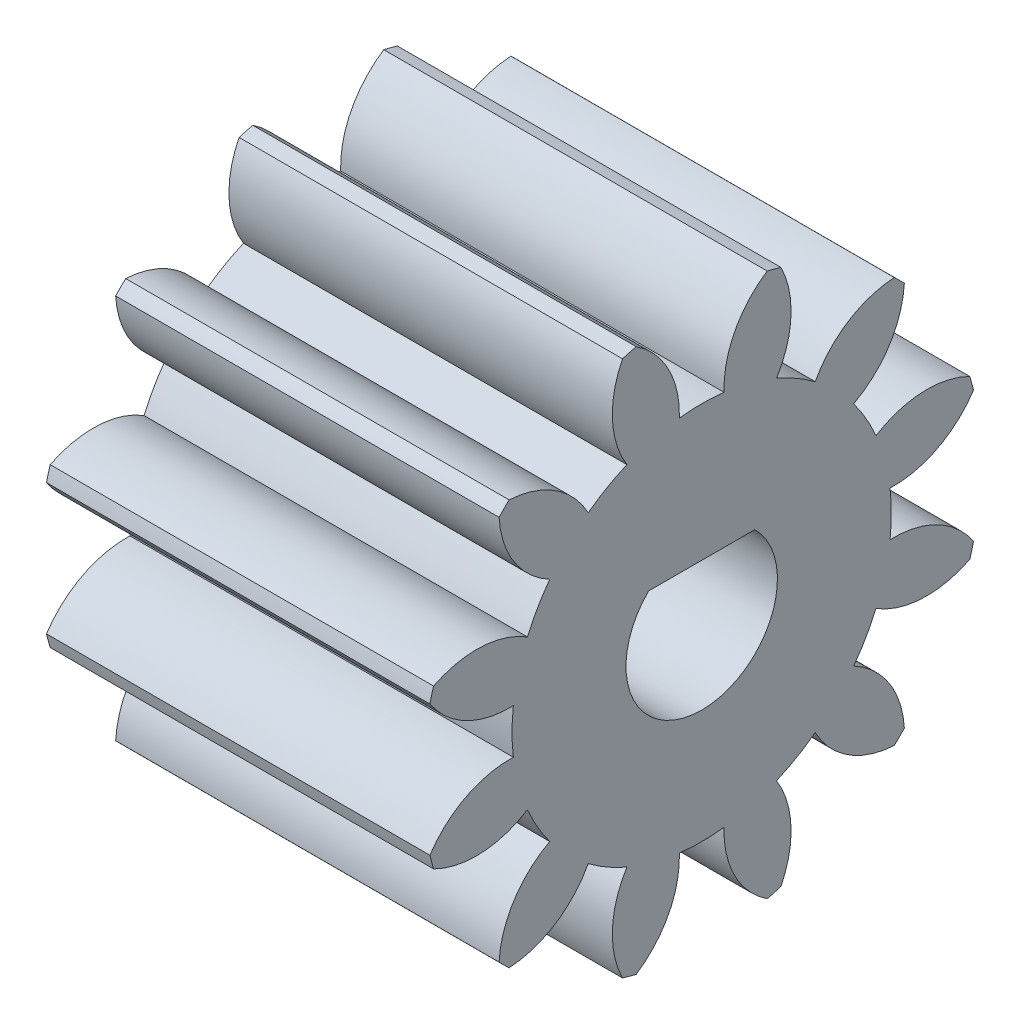
SolidWorks part; units mm, degrees
ref_plane "Plane1" through (0, 0, 0) normal (0, 0, 1) x (1, 0, 0)
ref_plane "Plane2" through (0, 0, 0) normal (0, 1, 0) x (1, 0, 0)
ref_plane "Plane3" through (0, 0, 0) normal (1, 0, 0) x (0, 0, -1)
sketch "HoldingSke" plane through (0, 0, 0) normal (0, 1, 0) x (1, 0, 0)
  line L0 (0, 0) -> (0.7825, -0.1663)
  line L1 (-15, 0) -> (100, 0) construction
  line L2 (0, 0) -> (-2.1039, 2.3779)
  line L3 (0, 0) -> (-11.863, 4.5341)
  line L4 (0, 0) -> (8.4473, 1.7955)
  line L5 (0, 0) -> (-46.8476, -17.4728)
  line L6 (0, 0) -> (-9.9476, -6.7116)
  line L7 (-2.1039, 2.3779) -> (8.6586, 51.2059)
  line L8 (-76.2, 54.61) -> (-76.1, 54.61)
  line L9 (-71.009, 38.7566) -> (-53.1078, 45.2721)
  line L10 (-76.2, 71.12) -> (104.1128, 71.12)
  line L11 (0, 0) -> (-12, 0)
  line L12 (-76.2, 101.6) -> (-76.155, 101.6)
  line L13 (24.9733, 27.94) -> (52.9518, 28.4284)
  line L14 (24.9733, 27.94) -> (24.9743, 27.94)
  line L15 (24.9733, 27.94) -> (100.4006, 29.5858)
  line L16 (-63.627, -1.25) -> (-12.827, -1.25)
  circle A0 centre (0, 0) radius 0.4
  circle A1 centre (0, 0) radius 5.9365
  circle A2 centre (0, 0) radius 37.5
  circle A3 centre (0, 0) radius 0.4
  dimension "MHD" = 11.873
  dimension "Hub_dia" = 75
  dimension "Bore" = 0.8
  dimension "MBD" = 0.8
  dimension "Num_teeth" = 12
  dimension "Pitch_radius" = 180.3128
  dimension "Pitch" = 0.8
  dimension "Width" = 12
  dimension "Overall_len" = 50
  dimension "Show_teeth" = 12
  dimension "Thickness" = 12
  dimension "OAL" = 50.0001
  dimension "T_dim" = 0.1
  dimension "Ap" = 20
  dimension "H" = 19.05
  dimension "Backlash" = 0.045
  dimension "Addendum_fac" = 1
  dimension "Dedendum_fac" = 1.25
  dimension "Clearance_fac" = 0.25
  dimension "Dedendum_add" = 0.001
  dimension "Module" = 1.25
sketch "BasProSke" plane through (0, 0, 0) normal (0, 1, 0) x (1, 0, 0)
  line L0 (-10, 0) -> (60, 0) construction
  line L1 (0, 0) -> (0, 8.75)
  line L2 (0, 0) -> (12, 0)
  line L3 (12, 0) -> (12, 8.75)
  line L4 (12, 8.75) -> (0, 8.75)
  dimension "Diameter" = 17.5
  dimension "Thickness" = 12
revolve "Base-Revolve" add sketch "BasProSke" angle 360 about L0
sketch "TooCutSke" plane through (0, 0, 0) normal (1, 0, 0) x (0, 0, -1)
  line L1 (0, 0) -> (0, 107) construction
  line L2 (0, 0) -> (-1.0576, 7.4251) construction
  line L3 (0, 0) -> (-3.8542, 14.3841) construction
  line L4 (-1.0576, 7.4251) -> (-1.9271, 7.1921) construction
  arc A0 (0.6993, 5.8952) -> (-0.6993, 5.8952) centre (0, 0) ccw
  arc A1 (2.0786, 8.5257) -> (-2.0786, 8.5257) centre (0, 0) ccw
  circle A2 centre (0, 0) radius 7.5 construction
  circle A3 centre (0, 0) radius 7.0477 construction
  arc A4 (-0.6993, 5.8952) -> (-2.0786, 8.5257) centre (-3.6975, 5.9999) ccw
  arc A5 (2.0786, 8.5257) -> (0.6993, 5.8952) centre (3.6975, 5.9999) ccw
  dimension "Root_dia" = 11.873
  dimension "Overcut_dia" = 17.5508
  dimension "Pitch_dia" = 15
  dimension "Base_dia" = 14.0954
  dimension "Flank_rad" = 3
  dimension "Half_ang" = 15
  dimension "Half_CT" = 0.9002
extrude "ToothCut" cut sketch "TooCutSke" along normal through all
fillet "Breaks" [suppressed] radius 0.025
fillet "RootFillets" [suppressed] radius 0.3135
pattern_circular "TeethCuts" count 12 every 30 about axis through (-10, 0, 0) along (1, 0, 0) of "ToothCut", "RootFillets", "Breaks"
sketch "HubNeaOneSke" plane through (0, 0, 0) normal (-1, 0, 0) x (0, 0, 1)
  circle A0 centre (0, 0) radius 5.9365
  dimension "Diameter" = 11.873
extrude "HubNearOne" [suppressed] add sketch "HubNeaOneSke" along normal blind 38.0001
sketch "HubNeaBotSke" plane through (0, 0, 0) normal (-1, 0, 0) x (0, 0, 1)
  circle A0 centre (0, 0) radius 5.9365
  dimension "Diameter" = 11.873
extrude "HubNearBoth" [suppressed] add sketch "HubNeaBotSke" along normal blind 19
ref_plane "FarPln" through (12, 0, 0) normal (1, 0, 0) x (0, 0, -1)
sketch "HubFarSke" plane through (12, 0, 0) normal (1, 0, 0) x (0, 0, -1)
  circle A0 centre (0, 0) radius 5.9365
  dimension "Diameter" = 11.873
extrude "HubFar" [suppressed] add sketch "HubFarSke" along normal blind 19
sketch "BorSke" plane through (0, 0, 0) normal (1, 0, 0) x (0, 0, -1)
  circle A0 centre (0, 0) radius 0.4
  dimension "Diameter" = 0.8
extrude "Bore" cut sketch "BorSke" along normal mid plane 100.0001
sketch "KeySke" plane through (0, 0, 0) normal (1, 0, 0) x (0, 0, -1)
  line L0 (-0.05, 0) -> (-0.05, 0.5)
  line L1 (-0.05, 0.5) -> (0.05, 0.5)
  line L2 (0.05, 0.5) -> (0.05, 0)
  line L3 (0, 0) -> (0, 34) construction
  line L4 (-0.05, 0) -> (0.05, 0)
  dimension "Offset" = 0.5
  dimension "Width" = 0.1
extrude "Keyway" [suppressed] cut sketch "KeySke" along normal mid plane 100.0001
pattern_circular "Keyway2" [suppressed] count 2 every 90 about axis through (-10, 0, 0) along (1, 0, 0)
sketch "Sketch1" plane through (12, 0, 0) normal (1, 0, 0) x (0, 0, -1)
  line L0 (-1.6616, 1.69) -> (1.6616, 1.69)
  arc A0 (-1.6616, 1.69) -> (1.6616, 1.69) centre (0, 0) ccw
  point P5 (0, -2.37)
  dimension "D1" = 4.74
  dimension "D2" = 4.06
extrude "Cut-Extrude1" cut sketch "Sketch1" against normal through all
equation "' \"Module@HoldingSke\" = 6.35"
equation "' \"Num_teeth@HoldingSke\" = 12"
equation "' \"Ap@HoldingSke\" =  20"
equation "' \"Width@HoldingSke\" = 0.5 * 25.4"
equation "' \"Hub_dia@HoldingSke\"= 1 * 25.4"
equation "' \"Overall_len@HoldingSke\" = 1.0 * 25.4"
equation "' \"Bore@HoldingSke\" = 0.75 * 25.4"
equation "' \"T_dim@HoldingSke\" = 0.1 * 25.4"
equation "' \"Width@KeySke\" = 0.25 * 25.4"
equation "' \"Show_teeth@HoldingSke\" = 13"
equation "' \"Backlash@HoldingSke\" = 0.009 * 25.4"
equation "' \"Addendum_fac@HoldingSke\" = 1.0"
equation "' \"Dedendum_fac@HoldingSke\" = 1.25"
equation "' \"Dedendum_add@HoldingSke\" = 0.00005 * 25.4"
equation "' \"Clearance_fac@HoldingSke\" = 0.25"
equation "\"Pitch@HoldingSke\" = 1 / \"Module@HoldingSke\""
equation "\"Overcut_dia@TooCutSke\" = (\"Num_teeth@HoldingSke\" + 2 * \"Addendum_fac@HoldingSke\") / \"Pitch@HoldingSke\" + 0.002 * 25.4"
equation "\"Pitch_dia@TooCutSke\" = \"Num_teeth@HoldingSke\" / \"Pitch@HoldingSke\""
equation "\"Base_dia@TooCutSke\" = \"Num_teeth@HoldingSke\" / \"Pitch@HoldingSke\" * cos((\"Ap@HoldingSke\"  * 3.14159265 / 180))"
equation "\"Root_dia@TooCutSke\" = (\"Num_teeth@HoldingSke\" + 2) / \"Pitch@HoldingSke\" - 2 * (\"Addendum_fac@HoldingSke\" + \"Dedendum_fac@HoldingSke\") / \"Pitch@HoldingSke\" - \"Dedendum_add@HoldingSke\" * 2"
equation "\"Half_ang@TooCutSke\" = 180 / \"Num_teeth@HoldingSke\""
equation "\"Half_CT@TooCutSke\" = \"Num_teeth@HoldingSke\" / \"Pitch@HoldingSke\" * sin((3.14159265 / 2 / \"Num_teeth@HoldingSke\")) / 2 - 7 * \"Backlash@HoldingSke\" / 4"
equation "\"Flank_rad@TooCutSke\" = \"Num_teeth@HoldingSke\" / \"Pitch@HoldingSke\" / 5"
equation "\"Radius@RootFillets\" = \"Clearance_fac@HoldingSke\" / \"Pitch@HoldingSke\" + \"Dedendum_add@HoldingSke\""
equation "\"Break_rad@Breaks\" = 0.02 / \"Pitch@HoldingSke\""
equation "\"Thickness@HoldingSke\" = \"Width@HoldingSke\""
equation "\"OAL@HoldingSke\" = \"Thickness@HoldingSke\""
equation "\"MHD@HoldingSke\" = (\"Num_teeth@HoldingSke\" + 2) / \"Pitch@HoldingSke\" - 2 * (\"Addendum_fac@HoldingSke\" + \"Dedendum_fac@HoldingSke\")  / \"Pitch@HoldingSke\" - \"Dedendum_add@HoldingSke\" * 2"
equation "\"MBD@HoldingSke\" = (\"Num_teeth@HoldingSke\" + 2) / \"Pitch@HoldingSke\" - 2 * (\"Addendum_fac@HoldingSke\" + \"Dedendum_fac@HoldingSke\")  / \"Pitch@HoldingSke\" - \"Dedendum_add@HoldingSke\" * 2 - 0.002 * 25.4"
equation "\"MHD@HoldingSke\" = ((sgn( \"MHD@HoldingSke\" - \"Hub_dia@HoldingSke\" )-1)*( \"MHD@HoldingSke\" - \"Hub_dia@HoldingSke\" ))/-2+ \"Hub_dia@HoldingSke\""
equation "\"MBD@HoldingSke\" = ((sgn( \"MBD@HoldingSke\" - \"Bore@HoldingSke\" )-1)*( \"MBD@HoldingSke\" - \"Bore@HoldingSke\" ))/-2+ \"Bore@HoldingSke\""
equation "\"OAL@HoldingSke\" = ((sgn( \"OAL@HoldingSke\" - \"Overall_len@HoldingSke\" )+1)*( \"OAL@HoldingSke\" - \"Overall_len@HoldingSke\" ))/2 + \"Overall_len@HoldingSke\" + 0.000002 * 25.4"
equation "\"Num_teeth@TeethCuts\" = int( \"Show_teeth@HoldingSke\" ) + 1"
equation "\"Num_teeth@TeethCuts\" = ((sgn( \"Num_teeth@TeethCuts\" - \"Num_teeth@HoldingSke\" )-1)*( \"Num_teeth@TeethCuts\" - \"Num_teeth@HoldingSke\" ))/-2+ \"Num_teeth@HoldingSke\""
equation "\"Num_teeth@TeethCuts\" = ((sgn( \"Num_teeth@TeethCuts\" - 2.0)+1)*( \"Num_teeth@TeethCuts\" - 2.0))/2 +2.0"
equation "\"Angle@TeethCuts\" = 360.0 / \"Num_teeth@HoldingSke\""
equation "\"Diameter@BasProSke\" = (\"Num_teeth@HoldingSke\" + 2 * \"Addendum_fac@HoldingSke\") / \"Pitch@HoldingSke\""
equation "\"Thickness@BasProSke\"  = \"Thickness@HoldingSke\""
equation "' \"Fillet_rad@BasProSke\" =  \"Thickness@HoldingSke\" * 0.05"
equation "\"MHD@HoldingSke\" = ((sgn( \"MHD@HoldingSke\" - \"Root_dia@TooCutSke\" )-1)*( \"MHD@HoldingSke\" - \"Root_dia@TooCutSke\" ))/-2+ \"Root_dia@TooCutSke\""
equation "\"Diameter@HubNeaOneSke\" = \"MHD@HoldingSke\""
equation "\"Length@HubNearOne\" = \"OAL@HoldingSke\" - \"Thickness@BasProSke\""
equation "\"Diameter@HubNeaBotSke\" = \"MHD@HoldingSke\""
equation "\"Length@HubNearBoth\" = ( \"OAL@HoldingSke\" - \"Thickness@BasProSke\" ) / 2.0"
equation "\"Thickness@FarPln\" = \"Thickness@BasProSke\""
equation "\"Diameter@HubFarSke\" = \"MHD@HoldingSke\""
equation "\"Length@HubFar\" = ( \"OAL@HoldingSke\" - \"Thickness@BasProSke\" ) / 2.0"
equation "\"Diameter@BorSke\" = \"MBD@HoldingSke\""
equation "\"D1@Bore\" = \"OAL@HoldingSke\" * 2.0"
equation "\"D1@Keyway\" = \"OAL@HoldingSke\" * 2.0"
equation "\"Offset@KeySke\" = \"T_dim@HoldingSke\" + \"MBD@HoldingSke\" / 2.0"
